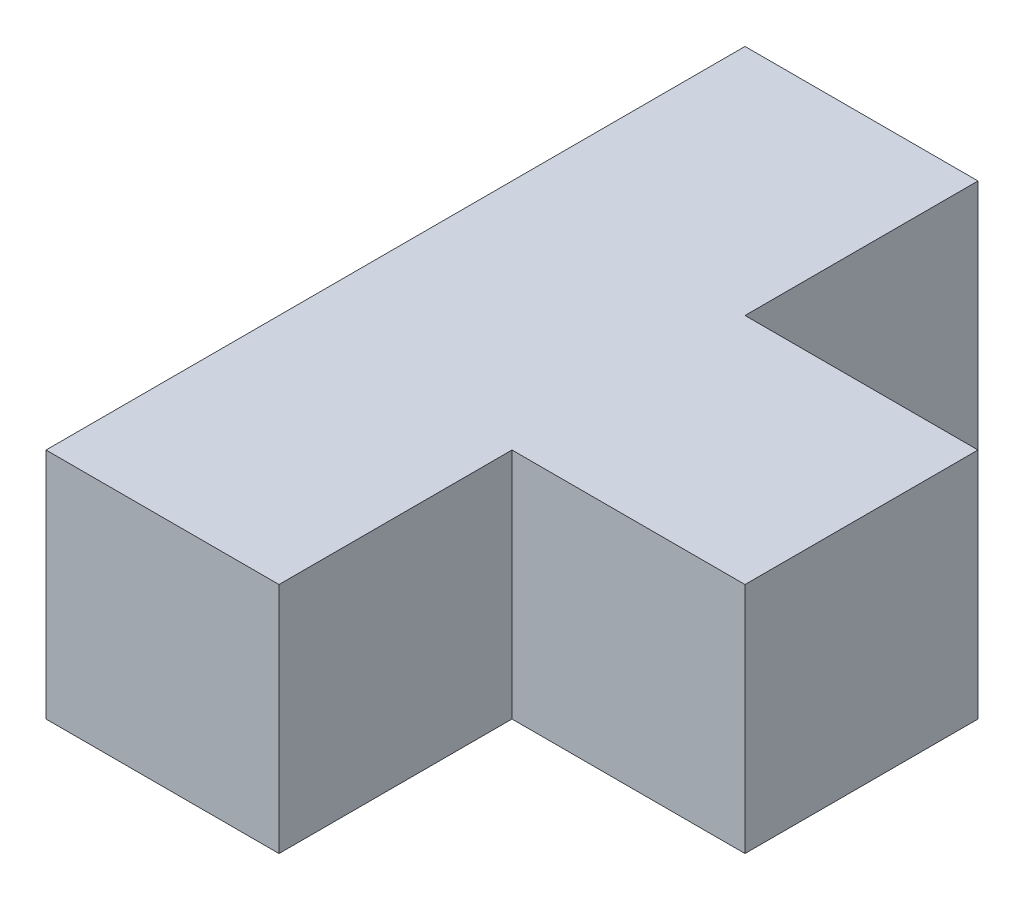
SolidWorks part; units mm, degrees
ref_plane "Front Plane" through (0, 0, 0) normal (0, 0, 1) x (1, 0, 0)
ref_plane "Top Plane" through (0, 0, 0) normal (0, 1, 0) x (1, 0, 0)
ref_plane "Right Plane" through (0, 0, 0) normal (1, 0, 0) x (0, 0, -1)
sketch "Sketch1" plane through (0, 0, 0) normal (0, 1, 0) x (1, 0, 0)
  line L0 (-5000, 7500) -> (-5000, -7500)
  line L1 (-5000, -7500) -> (0, -7500)
  line L2 (0, -7500) -> (0, -2500)
  line L3 (0, -2500) -> (5000, -2500)
  line L4 (5000, -2500) -> (5000, 2500)
  line L5 (5000, 2500) -> (0, 2500)
  line L6 (0, 2500) -> (0, 7500)
  line L7 (0, 7500) -> (-5000, 7500)
  dimension "D1" = 2500
  dimension "D2" = 2500
  dimension "D3" = 5000
  dimension "D4" = 5000
  dimension "D5" = 5000
  dimension "D6" = 5000
  dimension "D7" = 0
  dimension "D8" = 0
extrude "Boss-Extrude1" add sketch "Sketch1" along normal blind 5000
